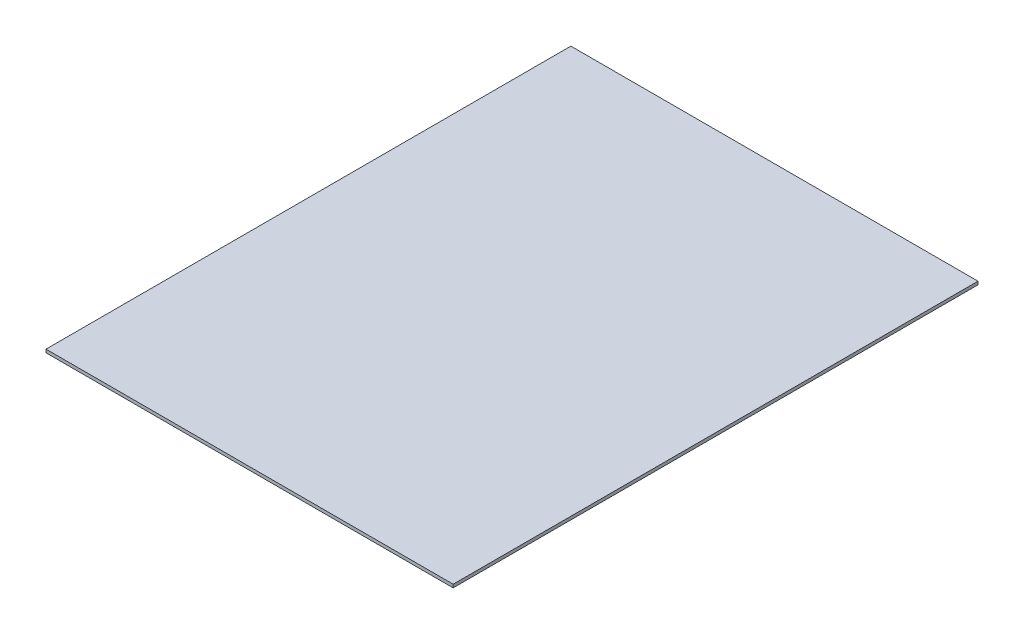
SolidWorks part; units mm, degrees
ref_plane "Front Plane" through (0, 0, 0) normal (0, 0, 1) x (1, 0, 0)
ref_plane "Top Plane" through (0, 0, 0) normal (0, 1, 0) x (1, 0, 0)
ref_plane "Right Plane" through (0, 0, 0) normal (1, 0, 0) x (0, 0, -1)
sketch "Sketch1" plane through (0, 0, 0) normal (0, 1, 0) x (1, 0, 0)
  line L1 (-666.9975, 646.3524) -> (613.0025, 646.3524)
  line L2 (-666.9975, 646.3524) -> (-666.9975, -1003.6476)
  line L3 (-666.9975, -1003.6476) -> (613.0025, -1003.6476)
  line L4 (613.0025, 646.3524) -> (613.0025, -1003.6476)
  dimension "D1" = 1280
  dimension "D2" = 1650
extrude "Boss-Extrude1" add sketch "Sketch1" along normal blind 10
